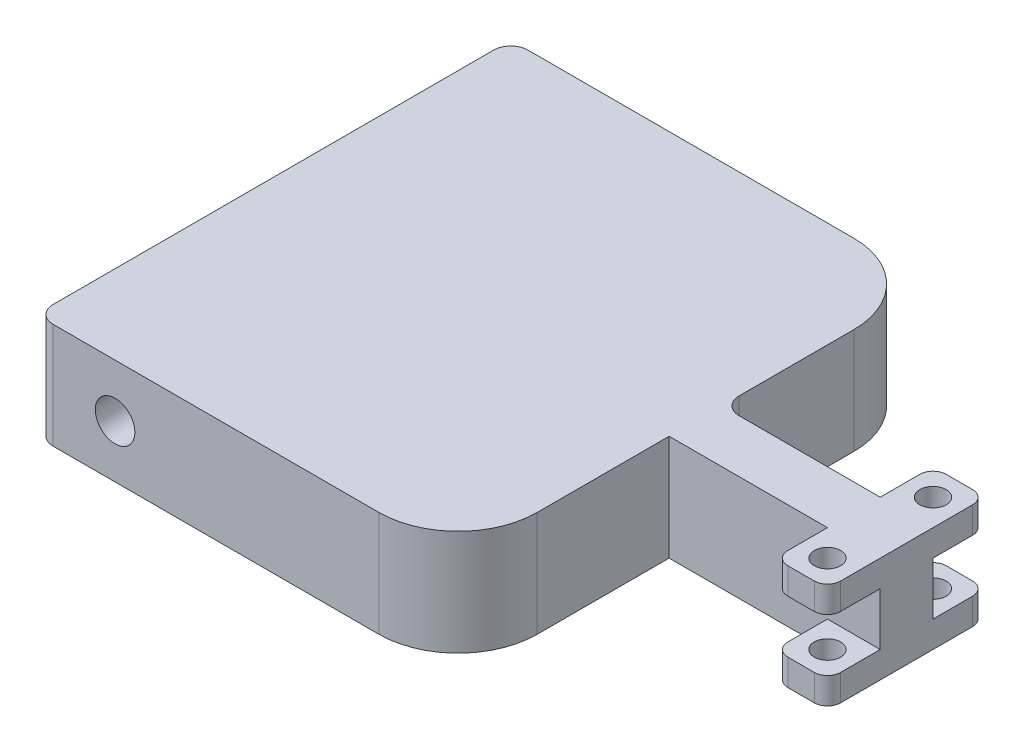
SolidWorks part; units mm, degrees
ref_plane "Front Plane" through (0, 0, 0) normal (0, 0, 1) x (1, 0, 0)
ref_plane "Top Plane" through (0, 0, 0) normal (0, 1, 0) x (1, 0, 0)
ref_plane "Right Plane" through (0, 0, 0) normal (1, 0, 0) x (0, 0, -1)
sketch "Sketch1" plane through (0, 0, 0) normal (0, 1, 0) x (1, 0, 0)
  line L0 (76.2, -25.4) -> (-76.2, -25.4)
  line L1 (-152.4, -228.6) -> (-482.6, -228.6)
  line L3 (-152.4, 228.6) -> (-482.6, 228.6)
  line L4 (-482.6, -228.6) -> (-482.6, 228.6)
  line L5 (53.6222, -25.4) -> (-482.6, 228.6) construction
  line L6 (53.6222, 25.4) -> (-482.6, -228.6) construction
  line L10 (-76.2, -152.4) -> (-76.2, -25.4)
  line L16 (76.2, -25.4) -> (76.2, -63.5)
  line L17 (88.9, -76.2) -> (114.3, -76.2)
  line L19 (0, 0) -> (127, 0) construction
  line L21 (88.9, 76.2) -> (114.3, 76.2)
  line L22 (76.2, 25.4) -> (76.2, 63.5)
  line L23 (-76.2, 152.4) -> (-76.2, 25.4)
  line L27 (76.2, 25.4) -> (-76.2, 25.4)
  line L29 (-741.372, 0) -> (837.4379, 0) construction
  line L30 (127, 63.5) -> (127, -63.5)
  arc A0 (76.2, -63.5) -> (88.9, -76.2) centre (88.9, -63.5) ccw
  arc A1 (127, -63.5) -> (114.3, -76.2) centre (114.3, -63.5) cw
  arc A2 (127, 63.5) -> (114.3, 76.2) centre (114.3, 63.5) ccw
  arc A3 (76.2, 63.5) -> (88.9, 76.2) centre (88.9, 63.5) cw
  arc A4 (-152.4, 228.6) -> (-76.2, 152.4) centre (-152.4, 152.4) cw
  arc A5 (-152.4, -228.6) -> (-76.2, -152.4) centre (-152.4, -152.4) ccw
  point P0 (0, 0)
  point P7 (0, 0)
  point P15 (0, 0)
  point P19 (76.2, -76.2)
  point P28 (0, 0)
  point P35 (76.2, 76.2)
  point P37 (-76.2, 228.6)
  point P40 (-76.2, -228.6)
  dimension "D8" = 12.7
  dimension "D9" = 12.7
  dimension "D11" = 76.2
  dimension "D1" = 457.2
  dimension "D2" = 203.2
  dimension "D3" = 203.2
  dimension "D4" = 76.2
  dimension "D5" = 152.4
  dimension "D7" = 50.8
  dimension "D10" = 482.6
extrude "Boss-Extrude1" add sketch "Sketch1" along normal mid plane 101.6
sketch "Sketch2" plane through (0, 0, 0) normal (0, 1, 0) x (1, 0, 0)
  line L1 (88.9, -76.2) -> (114.3, -76.2) construction
  line L2 (76.2, -25.4) -> (76.2, -63.5) construction
  line L3 (127, -63.5) -> (127, -25.4)
  line L4 (88.9, -76.2) -> (114.3, -76.2)
  line L5 (76.2, -25.4) -> (76.2, -63.5)
  line L6 (76.2, -25.4) -> (127, -25.4)
  line L7 (127, -63.5) -> (127, 63.5) construction
  line L8 (-76.2, -25.4) -> (76.2, -25.4) construction
  arc A0 (114.3, -76.2) -> (127, -63.5) centre (114.3, -63.5) ccw construction
  arc A1 (76.2, -63.5) -> (88.9, -76.2) centre (88.9, -63.5) ccw construction
  arc A2 (114.3, -76.2) -> (127, -63.5) centre (114.3, -63.5) ccw
  arc A3 (76.2, -63.5) -> (88.9, -76.2) centre (88.9, -63.5) ccw
extrude "Cut-Extrude1" cut sketch "Sketch2" against normal mid plane 50.8
sketch "Sketch3" plane through (0, 50.8, 0) normal (0, 1, 0) x (1, 0, 0)
  line L0 (88.9, -76.2) -> (114.3, -76.2) construction
  circle A0 centre (101.6, -50.8) radius 12.7
  point P4 (101.6, -76.2)
  dimension "D1" = 25.4
  dimension "D2" = 25.4
extrude "Cut-Extrude2" cut sketch "Sketch3" against normal through all both and the other way through all
mirror "Mirror1" about plane through (0, 0, 0) normal (0, 0, 1) of "Cut-Extrude2", "Cut-Extrude1"
sketch "Sketch4" plane through (0, 0, 228.6) normal (0, 0, 1) x (1, 0, 0)
  line L0 (88.9, -25.4) -> (114.3, -25.4) construction
  line L2 (-482.6, 50.8) -> (-152.4, 50.8) construction
  circle A0 centre (-406.4, 0) radius 19.05
  point P4 (101.6, -25.4)
  dimension "D1" = 38.1
  dimension "D2" = 508
  dimension "D3" = 50.8
extrude "Cut-Extrude3" cut sketch "Sketch4" against normal through all both and the other way through all
fillet "Fillet1" radius 16.51 3 edges at (-482.6, 0, -228.6) (-482.6, 0, 228.6) (-76.2, 0, -25.4)
